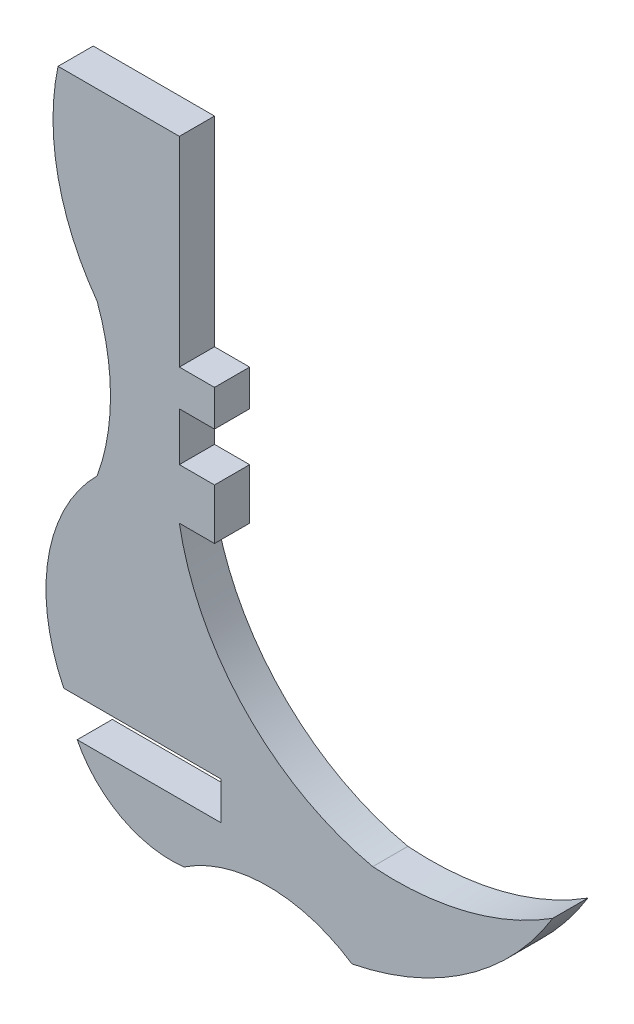
SolidWorks part; units mm, degrees
ref_plane "Front Plane" through (0, 0, 0) normal (0, 0, 1) x (1, 0, 0)
ref_plane "Top Plane" through (0, 0, 0) normal (0, 1, 0) x (1, 0, 0)
ref_plane "Right Plane" through (0, 0, 0) normal (1, 0, 0) x (0, 0, -1)
sketch "Sketch1" plane through (0, 0, 0) normal (0, 0, 1) x (1, 0, 0)
  line L0 (0, -1.9643) -> (-1.524, -1.9643)
  line L1 (0, -1.9643) -> (0, -4.1633)
  line L2 (0, -4.1633) -> (-1.524, -4.1633)
  line L3 (-1.524, -1.9643) -> (-1.524, 0.1321)
  line L4 (-1.524, 0.1321) -> (0, 0.1321)
  line L5 (0, 0.1321) -> (0, 1.6997)
  line L6 (0, 1.6997) -> (-1.524, 1.6997)
  line L7 (-1.524, 1.6997) -> (-1.524, 7.3084)
  line L8 (-1.524, 7.3084) -> (-1.524, 10.3651)
  line L9 (-1.524, 10.3651) -> (-6.7829, 10.3651)
  line L10 (-6.5363, -12.8665) -> (0.2854, -12.8665)
  line L11 (0.2854, -12.8665) -> (0.2854, -14.5088)
  line L12 (0.2854, -14.5088) -> (-5.955, -14.5088)
  arc A0 (-6.7829, 10.3651) -> (-5.0866, 2.384) centre (3.0263, 8.2791) ccw
  arc A1 (-5.0866, 2.384) -> (-5.0866, -4.1633) centre (-14.0881, -0.8897) cw
  arc A2 (-1.524, -4.1633) -> (6.861, -12.8665) centre (9.1894, -2.2324) ccw
  arc A3 (-5.0866, -4.1633) -> (-6.5363, -12.8665) centre (0.2854, -9.5305) ccw
  arc A4 (-5.955, -14.5088) -> (-1.3218, -16.9711) centre (-1.8845, -12.4398) ccw
  arc A5 (-1.3218, -16.9711) -> (5.96, -16.9711) centre (2.3191, -22.4356) cw
  arc A6 (5.96, -16.9711) -> (14.6665, -10.9052) centre (3.4033, -4.0201) ccw
  arc A7 (14.6665, -10.9052) -> (6.861, -12.8665) centre (7.8207, -0.1735) cw
extrude "Boss-Extrude1" add sketch "Sketch1" along normal blind 1.524
